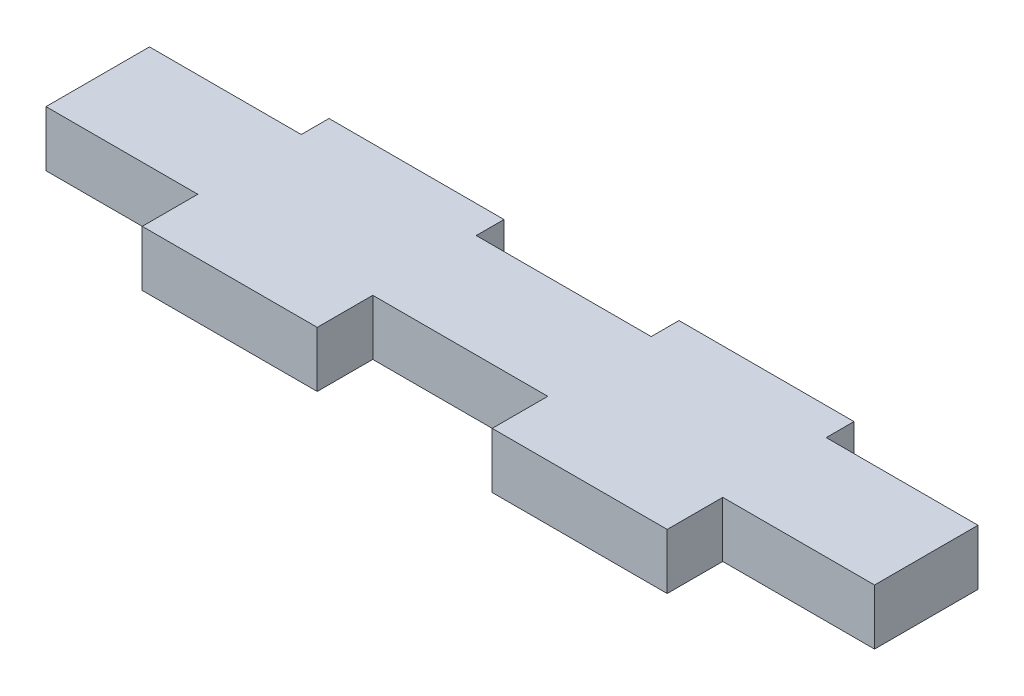
SolidWorks part; units mm, degrees
ref_plane "Front Plane" through (0, 0, 0) normal (0, 0, 1) x (1, 0, 0)
ref_plane "Top Plane" through (0, 0, 0) normal (0, 1, 0) x (1, 0, 0)
ref_plane "Right Plane" through (0, 0, 0) normal (1, 0, 0) x (0, 0, -1)
sketch "Sketch1" plane through (0, 0, 0) normal (0, 1, 0) x (1, 0, 0)
  line L1 (0, 0) -> (47.35, 0)
  line L2 (0, 0) -> (0, 10.675)
  line L3 (0, 10.675) -> (47.35, 10.675)
  line L4 (47.35, 0) -> (47.35, 10.675)
  dimension "D1" = 10.675
  dimension "D2" = 47.35
extrude "Boss-Extrude1" add sketch "Sketch1" along normal blind 3.175
sketch "Sketch2" plane through (0, 0, 0) normal (0, -1, 0) x (1, 0, 0)
  line L1 (0, 0) -> (47.35, 0) construction
  line L2 (47.35, 0) -> (38.675, 0)
  line L3 (47.35, 0) -> (47.35, -3.175)
  line L4 (47.35, -3.175) -> (38.675, -3.175)
  line L7 (38.675, 0) -> (38.675, -3.175)
  line L8 (0, -10.675) -> (0, 0) construction
  line L9 (28.675, 0) -> (18.675, 0)
  line L10 (28.675, 0) -> (28.675, -3.175)
  line L11 (28.675, -3.175) -> (18.675, -3.175)
  line L12 (18.675, 0) -> (18.675, -3.175)
  line L13 (8.675, -3.175) -> (0, -3.175)
  line L14 (8.675, -3.175) -> (8.675, 0)
  line L16 (8.675, 0) -> (0, 0)
  line L17 (0, -3.175) -> (0, 0)
  line L18 (47.35, -10.675) -> (0, -10.675) construction
  line L19 (47.35, -10.675) -> (38.675, -10.675)
  line L20 (47.35, -10.675) -> (47.35, -9.0875)
  line L21 (47.35, -9.0875) -> (38.675, -9.0875)
  line L22 (38.675, -10.675) -> (38.675, -9.0875)
  line L23 (47.35, 0) -> (47.35, -10.675) construction
  line L25 (28.675, -10.675) -> (18.675, -10.675)
  line L26 (28.675, -10.675) -> (28.675, -9.0875)
  line L27 (28.675, -9.0875) -> (18.675, -9.0875)
  line L28 (18.675, -10.675) -> (18.675, -9.0875)
  line L29 (8.675, -10.675) -> (0, -10.675)
  line L30 (8.675, -10.675) -> (8.675, -9.0875)
  line L31 (8.675, -9.0875) -> (0, -9.0875)
  line L32 (0, -10.675) -> (0, -9.0875)
  dimension "D1" = 8.675
  dimension "D2" = 1.5875
  dimension "D3" = 10
  dimension "D4" = 10
  dimension "D5" = 3.175
extrude "Cut-Extrude1" cut sketch "Sketch2" against normal through all
